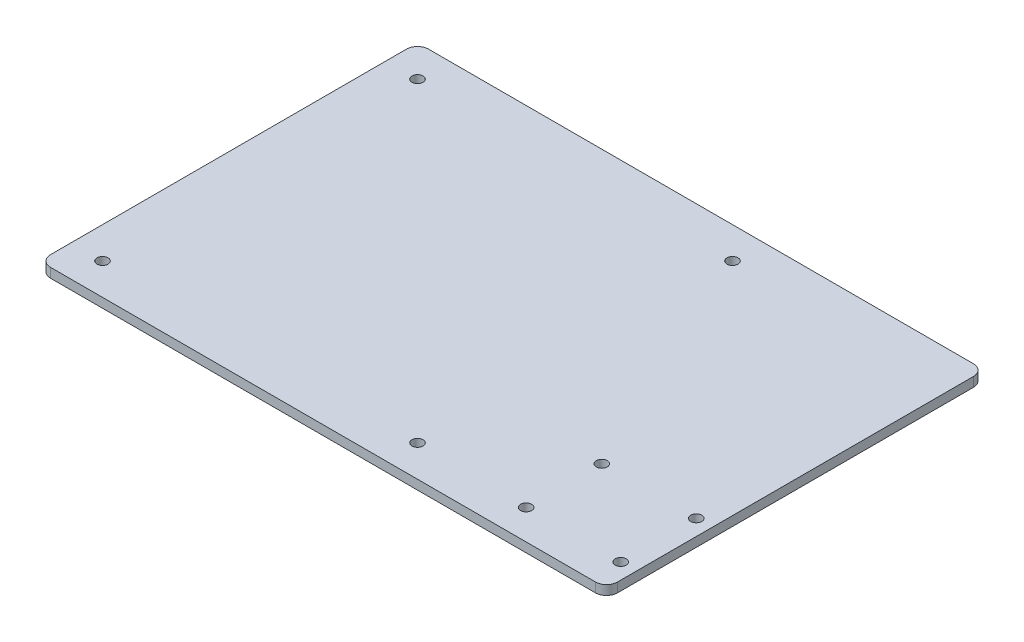
SolidWorks part; units mm, degrees
ref_plane "前视基准面" through (0, 0, 0) normal (0, 0, 1) x (1, 0, 0)
ref_plane "上视基准面" through (0, 0, 0) normal (0, 1, 0) x (1, 0, 0)
ref_plane "右视基准面" through (0, 0, 0) normal (1, 0, 0) x (0, 0, -1)
sketch "草图2" plane through (0, 0, 0) normal (0, 1, 0) x (1, 0, 0)
  line L1 (0, 0) -> (180, 0)
  line L2 (0, 0) -> (0, -120)
  line L3 (0, -120) -> (180, -120)
  line L4 (180, 0) -> (180, -120)
  dimension "D1" = 180
  dimension "D2" = 120
extrude "凸台-拉伸1" add sketch "草图2" along normal blind 3
fillet "圆角1" radius 3.5 4 edges at (0, 1.5, 120) (180, 1.5, 120) (180, 1.5, 0) (0, 1.5, 0)
sketch "草图3" plane through (0, 3, 0) normal (0, 1, 0) x (1, 0, 0)
  line L0 (3.5, -120) -> (176.5, -120) construction
  line L1 (175, -110.5) -> (145, -110.5) construction
  line L2 (175, -110.5) -> (175, -86.5) construction
  line L3 (175, -86.5) -> (145, -86.5) construction
  line L4 (145, -110.5) -> (145, -86.5) construction
  line L5 (180, -116.5) -> (180, -3.5) construction
  circle A0 centre (175, -110.5) radius 1.75
  circle A1 centre (145, -110.5) radius 1.75
  circle A2 centre (175, -86.5) radius 1.75
  circle A3 centre (145, -86.5) radius 1.75
  dimension "D5" = 3.5
  dimension "D6" = 3.5
  dimension "D7" = 3.5
  dimension "D8" = 3.5
  dimension "D1" = 30
  dimension "D2" = 24
  dimension "D3" = 9.5
  dimension "D4" = 5
extrude "切除-拉伸1" cut sketch "草图3" against normal through all
sketch "草图4" plane through (0, 3, 0) normal (0, 1, 0) x (1, 0, 0)
  line L0 (3.5, -120) -> (176.5, -120) construction
  line L1 (110, -110) -> (10, -110) construction
  line L2 (110, -110) -> (110, -10) construction
  line L3 (110, -10) -> (10, -10) construction
  line L4 (10, -110) -> (10, -10) construction
  line L5 (0, -3.5) -> (0, -116.5) construction
  line L6 (168.1233, -60) -> (-112.5838, -60) construction
  line L7 (60, -129.0664) -> (60, 23.9873) construction
  circle A0 centre (110, -110) radius 1.75
  circle A1 centre (110, -10) radius 1.75
  circle A2 centre (10, -10) radius 1.75
  circle A3 centre (10, -110) radius 1.75
  dimension "D5" = 3.5
  dimension "D1" = 100
  dimension "D2" = 100
  dimension "D3" = 10
  dimension "D4" = 10
extrude "切除-拉伸2" cut sketch "草图4" against normal through all
